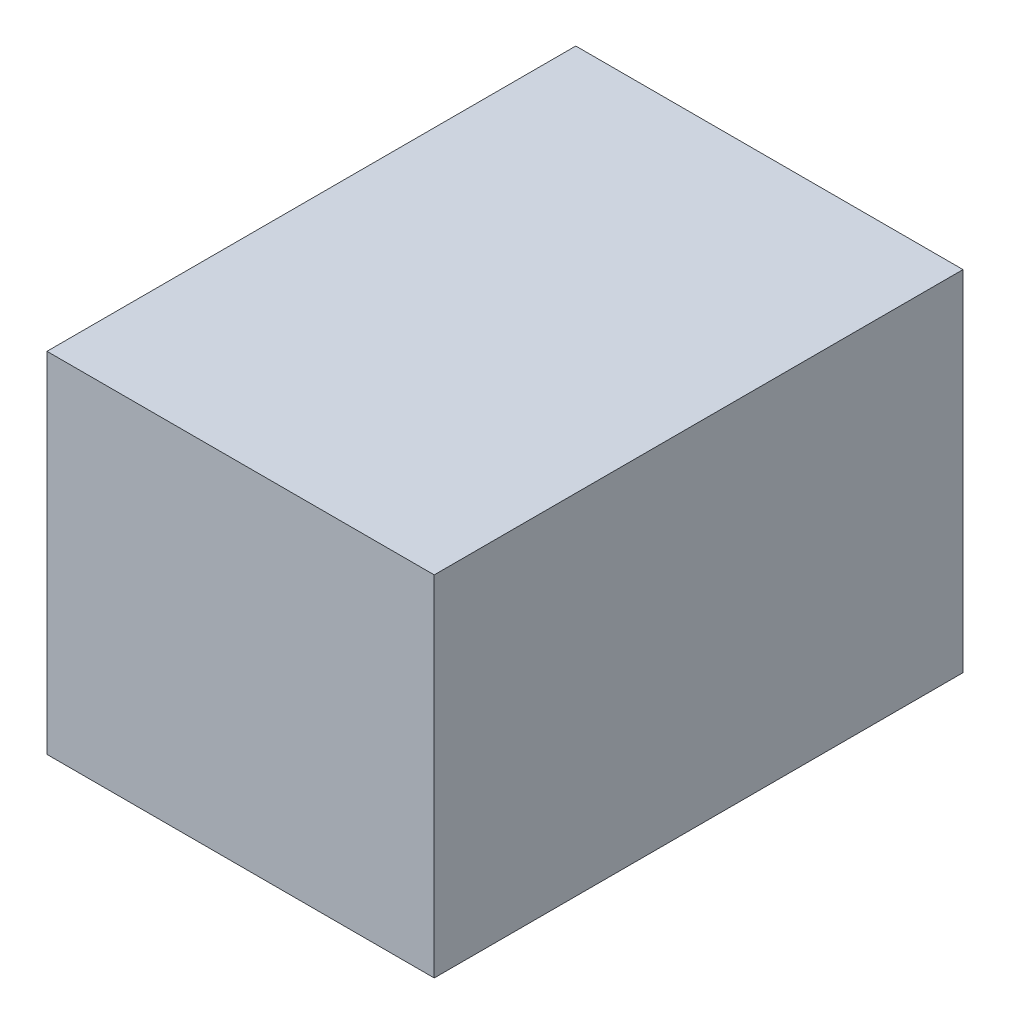
SolidWorks part; units mm, degrees
material "Brass"
ref_plane "Front Plane" through (0, 0, 0) normal (0, 0, 1) x (1, 0, 0)
ref_plane "Top Plane" through (0, 0, 0) normal (0, 1, 0) x (1, 0, 0)
ref_plane "Right Plane" through (0, 0, 0) normal (1, 0, 0) x (0, 0, -1)
sketch "Sketch1" plane through (0, 0, 0) normal (0, 1, 0) x (1, 0, 0)
  line L1 (0, 0) -> (12.0904, 0)
  line L2 (0, 0) -> (0, 16.51)
  line L3 (0, 16.51) -> (12.0904, 16.51)
  line L4 (12.0904, 0) -> (12.0904, 16.51)
  dimension "D1" = 12.0904
  dimension "D2" = 16.51
extrude "Boss-Extrude1" add sketch "Sketch1" along normal blind 10.9
